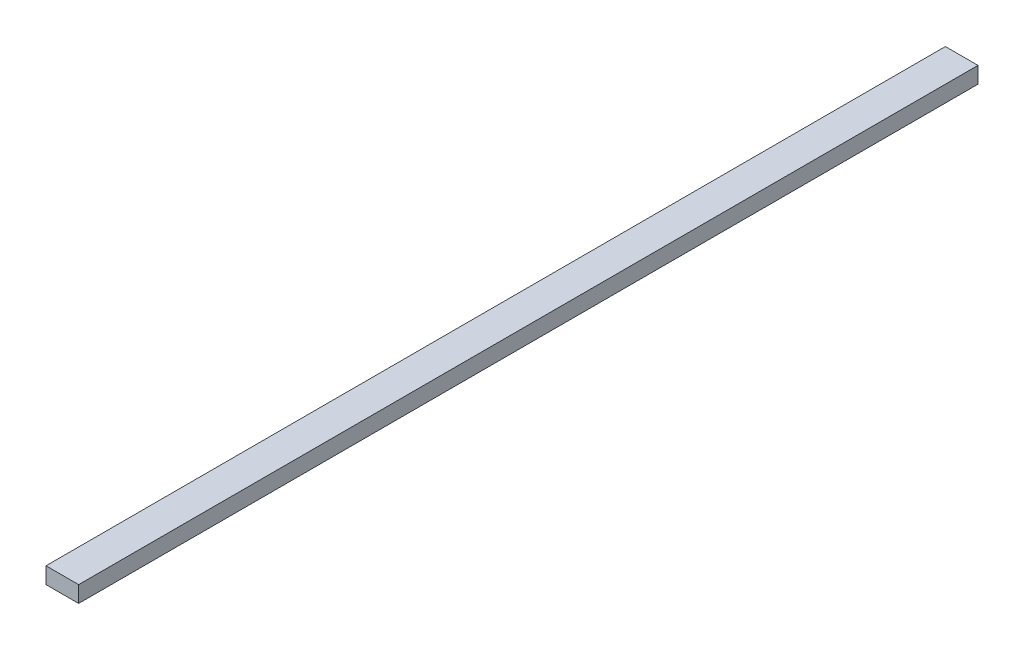
SolidWorks part; units mm, degrees
ref_plane "Alzado" through (0, 0, 0) normal (0, 0, 1) x (1, 0, 0)
ref_plane "Planta" through (0, 0, 0) normal (0, 1, 0) x (1, 0, 0)
ref_plane "Vista lateral" through (0, 0, 0) normal (1, 0, 0) x (0, 0, -1)
sketch "Croquis1" plane through (0, 0, 0) normal (0, 0, 1) x (1, 0, 0)
  line L1 (12.7, -6.35) -> (-12.7, -6.35)
  line L2 (12.7, -6.35) -> (12.7, 6.35)
  line L3 (12.7, 6.35) -> (-12.7, 6.35)
  line L4 (-12.7, -6.35) -> (-12.7, 6.35)
  line L5 (12.7, -6.35) -> (-12.7, 6.35) construction
  line L6 (12.7, 6.35) -> (-12.7, -6.35) construction
  point P0 (0, 0)
  dimension "D1" = 25.4
  dimension "D2" = 12.7
extrude "Saliente-Extruir1" add sketch "Croquis1" against normal blind 700
